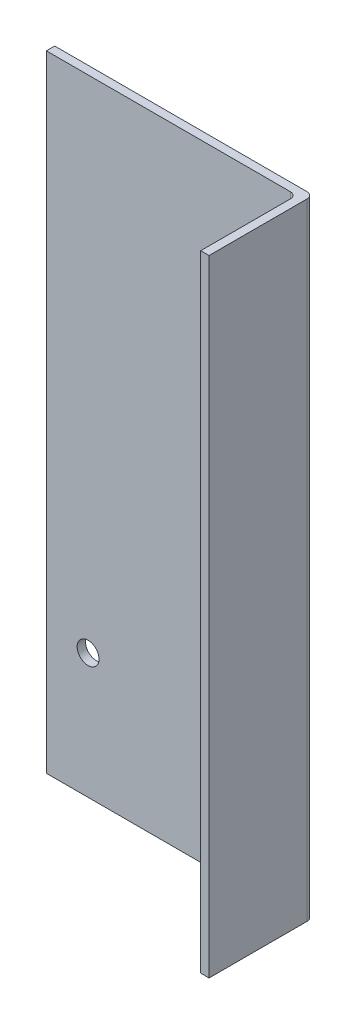
SolidWorks part; units mm, degrees
ref_plane "Front Plane" through (0, 0, 0) normal (0, 0, 1) x (1, 0, 0)
ref_plane "Top Plane" through (0, 0, 0) normal (0, 1, 0) x (1, 0, 0)
ref_plane "Right Plane" through (0, 0, 0) normal (1, 0, 0) x (0, 0, -1)
sketch "Sketch1" plane through (0, 0, 0) normal (0, 1, 0) x (1, 0, 0)
  line L1 (-60, 2) -> (60, 2)
  line L2 (-60, 2) -> (-60, -2)
  line L3 (-60, -2) -> (60, -2)
  line L4 (60, 2) -> (60, -2)
  line L5 (-60, 2) -> (60, -2) construction
  line L6 (-60, -2) -> (60, 2) construction
  line L7 (60, 2) -> (64, 2)
  line L8 (60, 2) -> (60, -48)
  line L9 (60, -48) -> (64, -48)
  line L10 (64, 2) -> (64, -48)
  point P0 (0, 0)
  dimension "D1" = 4
  dimension "D2" = 120
  dimension "D3" = 50
extrude "Extrude" add sketch "Sketch1" along normal blind 300 contours L10 L7 L4 L8 L9 | L4 L1 L2 L3
fillet "Fillet" radius 3
sketch "Sketch2" plane through (0, 0, 2) normal (0, 0, 1) x (1, 0, 0)
  line L0 (-60, 240) -> (60, 240) construction
  line L1 (-60, 300) -> (-60, 0) construction
  line L2 (60, 300) -> (60, 0) construction
  line L3 (0, 300) -> (0, 0) construction
  line L4 (-60, 300) -> (57, 300) construction
  line L7 (60, 150) -> (-60, 150) construction
  line L8 (60, 300) -> (60, 0) construction
  line L9 (-60, 300) -> (57, 300) construction
  circle A0 centre (-40, 240) radius 5.25
  circle A1 centre (40, 240) radius 5.25
  dimension "D1" = 10.5
  dimension "D2" = 80
  dimension "D3" = 60
extrude "Holes right" [suppressed] cut sketch "Sketch2" against normal up to next
sketch "Sketch3" plane through (0, 0, 2) normal (0, 0, 1) x (1, 0, 0)
  line L0 (0, 0) -> (0, 300) construction
  line L1 (-60, 300) -> (57, 300) construction
  line L2 (-60, 60) -> (64, 60) construction
  line L3 (-60, 300) -> (-60, 0) construction
  line L4 (64, 300) -> (64, 0) construction
  line L5 (-60, 0) -> (57, 0) construction
  circle A0 centre (-40, 60) radius 5.25
  circle A1 centre (40, 60) radius 5.25
  dimension "D2" = 10.5
  dimension "D3" = 80
  dimension "D1" = 60
extrude "Holes left" cut sketch "Sketch3" against normal up to next
